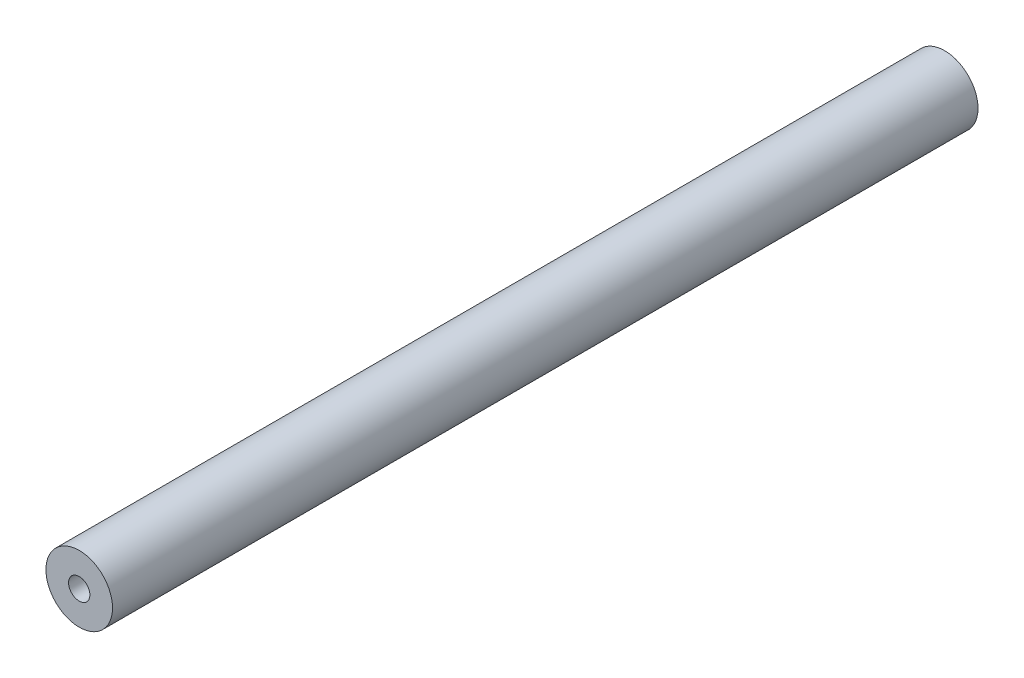
SolidWorks part; units mm, degrees
ref_plane "Front Plane" through (0, 0, 0) normal (0, 0, 1) x (1, 0, 0)
ref_plane "Top Plane" through (0, 0, 0) normal (0, 1, 0) x (1, 0, 0)
ref_plane "Right Plane" through (0, 0, 0) normal (1, 0, 0) x (0, 0, -1)
sketch "Sketch1" plane through (0, 0, 0) normal (0, 0, 1) x (1, 0, 0)
  circle A1 centre (0, 0) radius 2.032
  circle A2 centre (0, 0) radius 6.35
  dimension "D2" = 4.064
extrude "Boss-Extrude1" add sketch "Sketch1" along normal blind 165.1
